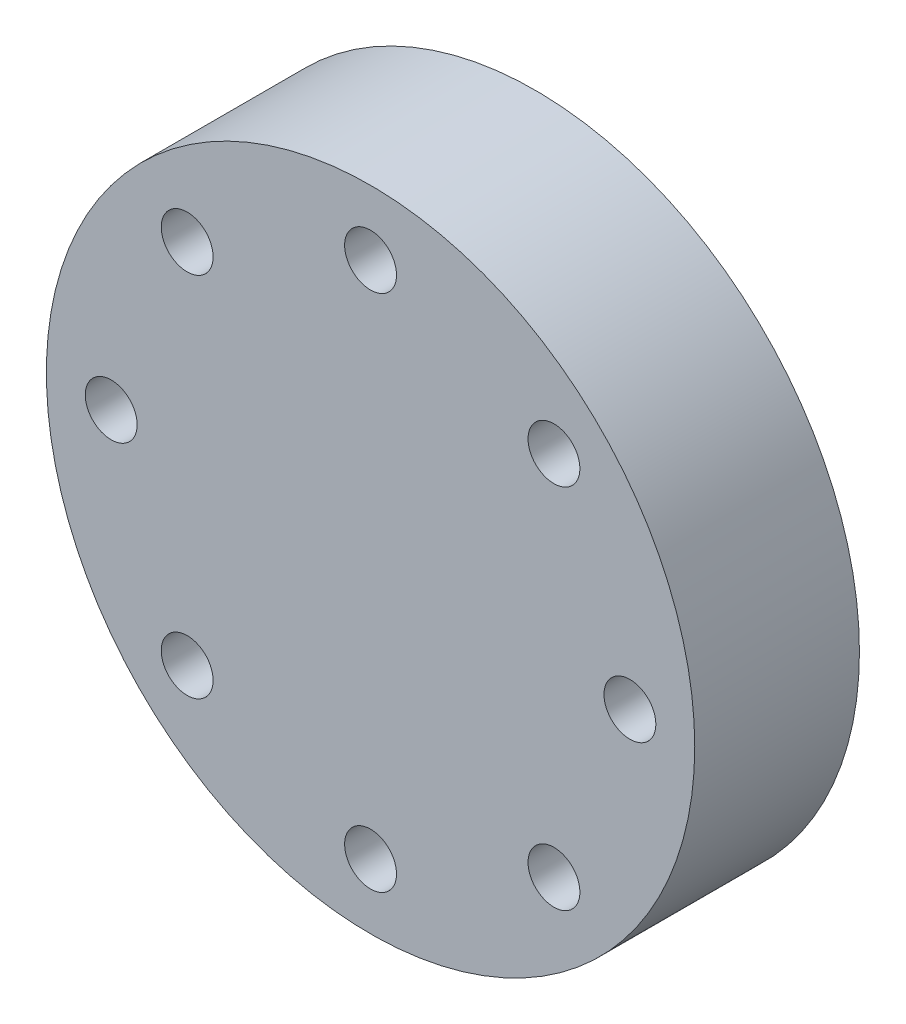
SolidWorks part; units mm, degrees
ref_plane "Plano frontal" through (0, 0, 0) normal (0, 0, 1) x (1, 0, 0)
ref_plane "Plano superior" through (0, 0, 0) normal (0, 1, 0) x (1, 0, 0)
ref_plane "Plano direito" through (0, 0, 0) normal (1, 0, 0) x (0, 0, -1)
sketch "Esboço1" plane through (0, 0, 0) normal (0, 0, 1) x (1, 0, 0)
  line L0 (0, -1000) -> (0, 49000) construction
  circle A0 centre (0, 0) radius 50
  circle A1 centre (0, 0) radius 40 construction
  circle A2 centre (0, 40) radius 4
  circle A3 centre (28.2843, 28.2843) radius 4
  circle A4 centre (40, 0) radius 4
  circle A5 centre (28.2843, -28.2843) radius 4
  circle A6 centre (0, -40) radius 4
  circle A7 centre (-28.2843, -28.2843) radius 4
  circle A8 centre (-40, 0) radius 4
  circle A9 centre (-28.2843, 28.2843) radius 4
  point P25 (0, 0)
  dimension "D1" = 100
  dimension "D2" = 80
  dimension "D3" = 8
  dimension "D4" = 8
extrude "Ressalto-extrusão1" add sketch "Esboço1" along normal blind 25.4
